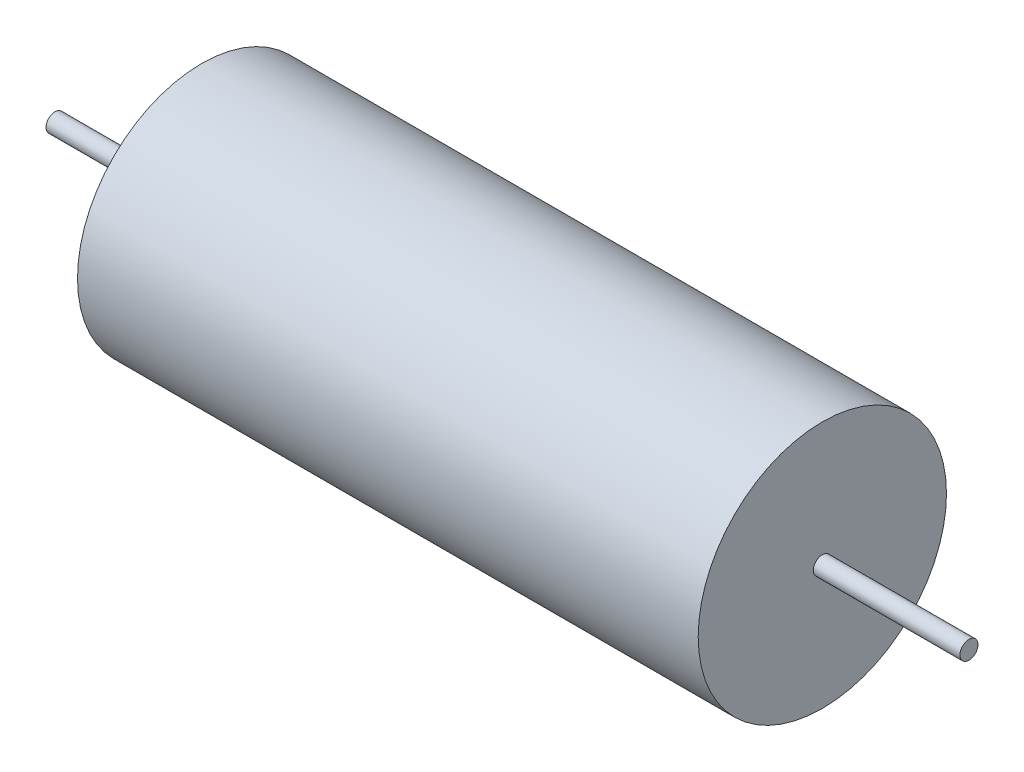
SolidWorks part; units mm, degrees
ref_plane "Front Plane" through (0, 0, 0) normal (0, 0, 1) x (1, 0, 0)
ref_plane "Top Plane" through (0, 0, 0) normal (0, 1, 0) x (1, 0, 0)
ref_plane "Right Plane" through (0, 0, 0) normal (1, 0, 0) x (0, 0, -1)
sketch "Sketch1" plane through (0, 0, 0) normal (0, 0, 1) x (1, 0, 0)
  line L0 (-93.5, 0) -> (-93.5, 1.85)
  line L1 (55, 0) -> (-55, 0) construction
  line L2 (-93.5, 1.85) -> (-63.5, 1.85)
  line L3 (-63.5, 1.85) -> (-63.5, 25.4)
  line L4 (-63.5, 25.4) -> (63.5, 25.4)
  line L5 (63.5, 25.4) -> (63.5, 1.85)
  line L6 (63.5, 1.85) -> (93.5, 1.85)
  line L7 (93.5, 1.85) -> (93.5, 0)
  line L8 (93.5, 0) -> (-93.5, 0)
  line L10 (0, -55) -> (0, 55) construction
  point P10 (93.0125, 25.4)
  point P11 (0, 0)
  dimension "D1" = 25.4
  dimension "D2" = 127
  dimension "D3" = 1.85
  dimension "D4" = 30
revolve "Revolve1" add sketch "Sketch1" angle 360 about L8
